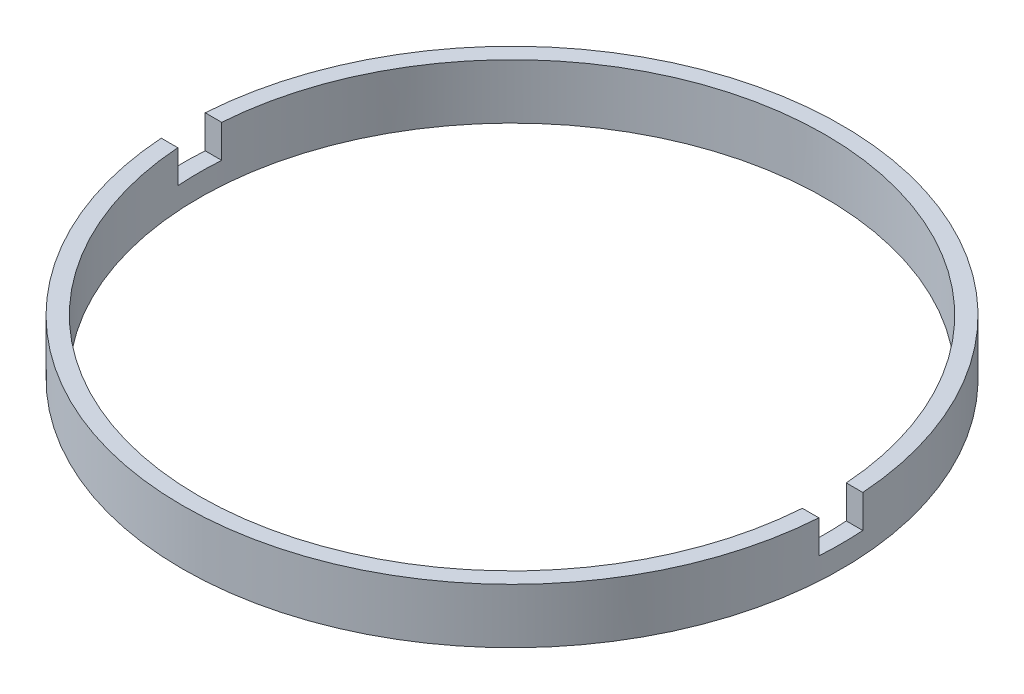
SolidWorks part; units mm, degrees
ref_plane "前视基准面" through (0, 0, 0) normal (0, 0, 1) x (1, 0, 0)
ref_plane "上视基准面" through (0, 0, 0) normal (0, 1, 0) x (1, 0, 0)
ref_plane "右视基准面" through (0, 0, 0) normal (1, 0, 0) x (0, 0, -1)
sketch "草图1" plane through (0, 0, 0) normal (0, 0, 1) x (1, 0, 0)
  line L0 (0, 56.2608) -> (0, -99.1922) construction
  line L1 (14.25, -1.9642) -> (15, -1.9642)
  line L4 (15, -1.9642) -> (15, -4.4642)
  line L5 (14.25, -4.4642) -> (14.25, -1.9642)
  line L7 (14.25, -4.4642) -> (15, -4.4642)
  dimension "D1" = 2.5
  dimension "D2" = 15
  dimension "D3" = 14.25
revolve "旋转1" add sketch "草图1" angle 360 about L0
cosmetic thread "装饰螺纹线1" parameters "D2"=29.99
sketch "草图2" plane through (0, -1.9642, 0) normal (0, 1, 0) x (1, 0, 0)
  line L0 (-28.67, 0) -> (29.9422, 0) construction
  line L2 (-26.8525, 1) -> (26.8525, 1)
  line L3 (-26.8525, 1) -> (-26.8525, -1)
  line L4 (-26.8525, -1) -> (26.8525, -1)
  line L5 (26.8525, 1) -> (26.8525, -1)
  line L6 (-26.8525, 1) -> (26.8525, -1) construction
  line L7 (-26.8525, -1) -> (26.8525, 1) construction
  point P3 (0, 0)
  dimension "D1" = 2
extrude "切除-拉伸1" cut sketch "草图2" against normal blind 1.5
